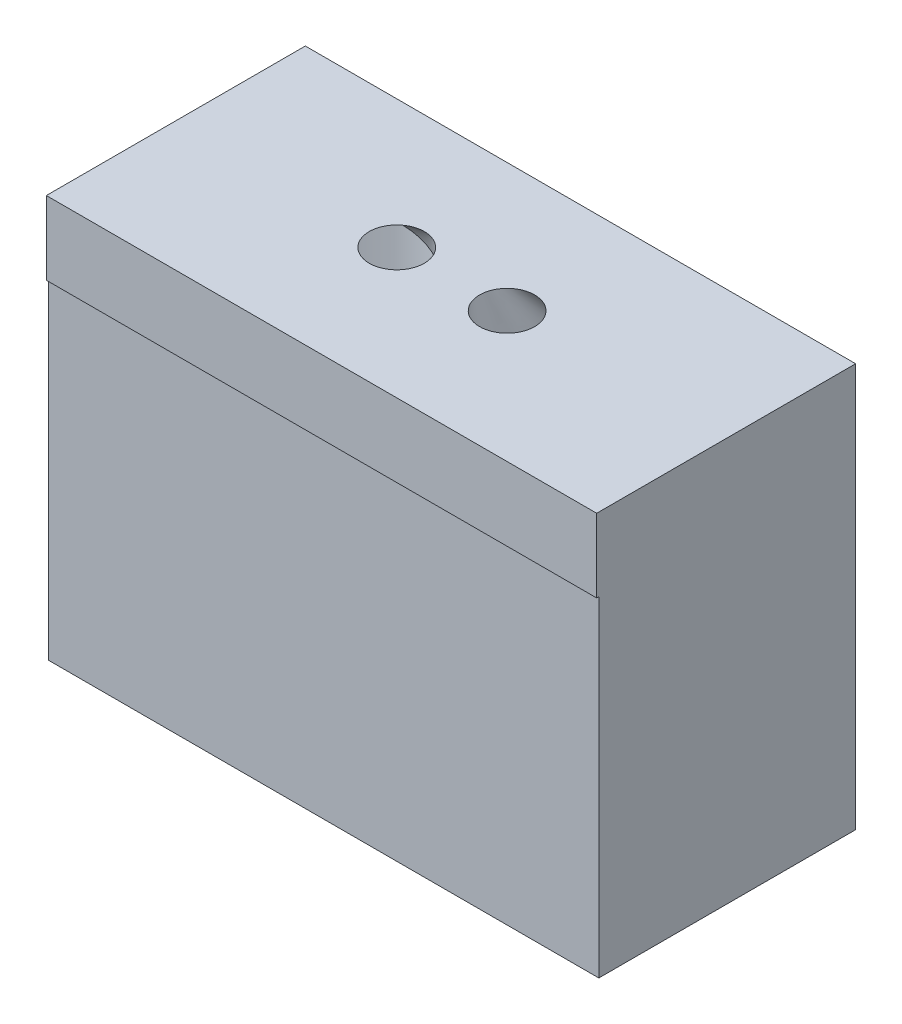
SolidWorks part; units mm, degrees
ref_plane "Alzado" through (0, 0, 0) normal (0, 0, 1) x (1, 0, 0)
ref_plane "Planta" through (0, 0, 0) normal (0, 1, 0) x (1, 0, 0)
ref_plane "Vista lateral" through (0, 0, 0) normal (1, 0, 0) x (0, 0, -1)
sketch "Croquis1" plane through (0, 0, 0) normal (0, 1, 0) x (1, 0, 0)
  line L0 (0, 0) -> (-8, 0) construction
  line L2 (-11.5, -3.5) -> (3.5, -3.5)
  line L3 (-11.5, -3.5) -> (-11.5, 3.5)
  line L4 (-11.5, 3.5) -> (3.5, 3.5)
  line L5 (3.5, -3.5) -> (3.5, 3.5)
  line L6 (-11.5, -3.5) -> (3.5, 3.5) construction
  line L7 (-11.5, 3.5) -> (3.5, -3.5) construction
  circle A0 centre (0, 0) radius 2.6
  circle A1 centre (0, 0) radius 3
  circle A2 centre (-8, 0) radius 2.6
  circle A3 centre (-8, 0) radius 3
  point P7 (-4, 0)
  point P12 (3.5, 0)
  dimension "D1" = 5.2
  dimension "D2" = 6
  dimension "D5" = 8
  dimension "D6" = 3.5
  dimension "D7" = 3.5
extrude "Saliente-Extruir1" add sketch "Croquis1" along normal blind 9 contours L3 L2 L5 L4 | A2 | A0
sketch "Croquis2" plane through (0, 0, 0) normal (0, -1, 0) x (1, 0, 0)
  circle A0 centre (0, 0) radius 3
  circle A1 centre (-8, 0) radius 3
  dimension "D1" = 6
extrude "Cortar-Extruir1" cut sketch "Croquis2" against normal blind 1
sketch "Croquis3" plane through (0, 9, 0) normal (0, 1, 0) x (1, 0, 0)
  line L0 (-11.5, 3.5) -> (3.5, 3.5)
  line L1 (-11.5, 3.5) -> (-11.5, -3.5587)
  line L2 (3.5, 3.5) -> (3.5, -3.5587)
  line L3 (-11.5, -3.5587) -> (3.5, -3.5587)
extrude "Saliente-Extruir2" add sketch "Croquis3" along normal blind 2
sketch "Croquis4" plane through (0, 11, 0) normal (0, 1, 0) x (1, 0, 0)
  line L0 (-11.5, 3.5) -> (3.5, -3.5587) construction
  line L1 (3.5, 3.5) -> (-11.5, -3.5587) construction
  line L2 (-9.346, 0.0019) -> (3.5, -0.0294) construction
  line L3 (3.5, -3.5587) -> (3.5, 3.5) construction
  circle A0 centre (-5.5, -0.0075) radius 0.75
  point P14 (-4, -0.0294)
  dimension "D1" = 1.5
  dimension "D2" = 1.5
loft "Cortar-Recubrir3" cut profiles "Croquis4" section "Croquis4" section face at (-8, 9, 2.6)
ref_plane "Plano2" through (-4, 0, 0) normal (1, 0, 0) x (0, 0, -1)
sketch "Croquis9" plane through (0, 11, 0) normal (0, 1, 0) x (1, 0, 0)
  line L0 (-4, -3.8823) -> (-4, 3.8823) construction
  circle A0 centre (-2.5, 0) radius 0.75
  point P4 (0, 0)
  dimension "D1" = 1.5
  dimension "D2" = 1.5
loft "Cortar-Recubrir4" cut profiles "Croquis9" section "Croquis9" section face at (0, 9, 2.6)
